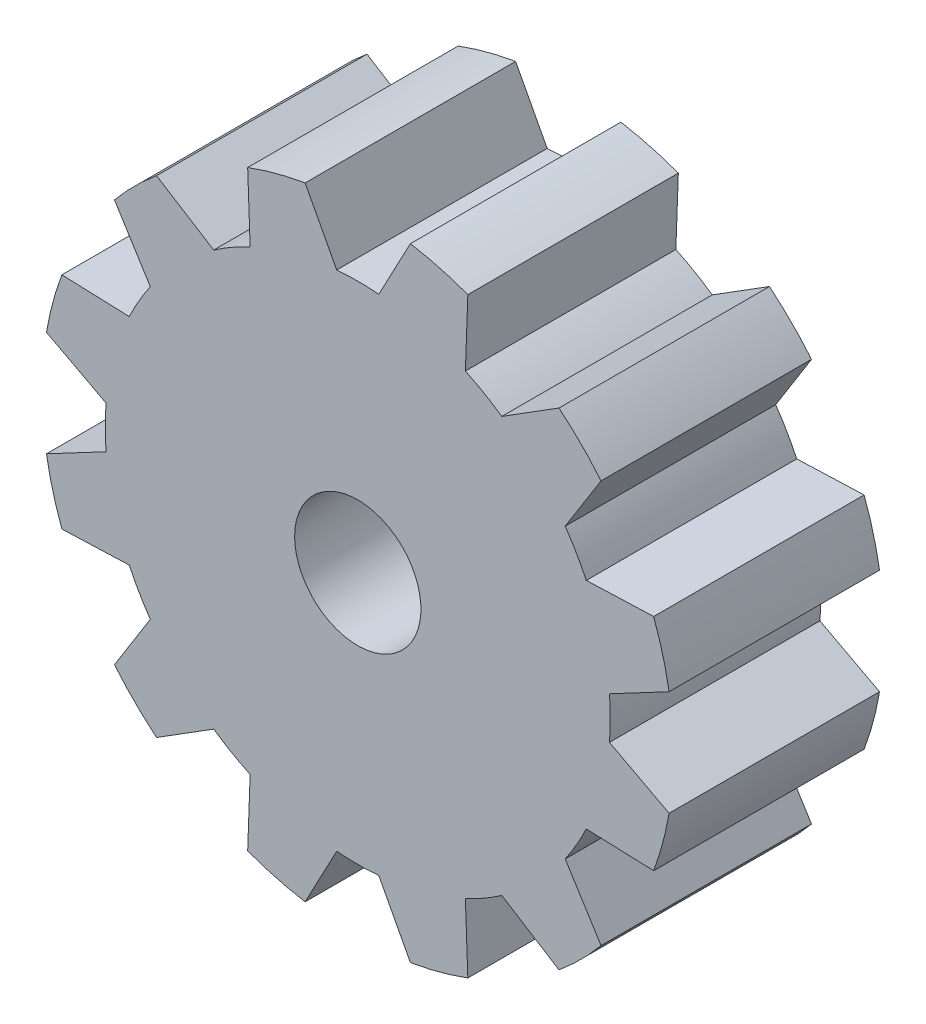
SolidWorks part; units mm, degrees
ref_plane "Front Plane" through (0, 0, 0) normal (0, 0, 1) x (1, 0, 0)
ref_plane "Top Plane" through (0, 0, 0) normal (0, 1, 0) x (1, 0, 0)
ref_plane "Right Plane" through (0, 0, 0) normal (1, 0, 0) x (0, 0, -1)
sketch "Sketch1" plane through (0, 0, 0) normal (0, 0, 1) x (1, 0, 0)
  circle A0 centre (0, 0) radius 15
  dimension "D1" = 30
extrude "Boss-Extrude1" add sketch "Sketch1" along normal blind 10
sketch "Sketch2" plane through (0, 0, 10) normal (0, 0, 1) x (1, 0, 0)
  line L0 (-1, 11.9583) -> (-2.5, 14.7902)
  line L1 (1, 11.9583) -> (2.5, 14.7902)
  line L2 (0, 0) -> (0, 15) construction
  line L3 (-2.5, 14.7902) -> (2.5, 14.7902) construction
  line L4 (1, 11.9583) -> (-1, 11.9583) construction
  circle A0 centre (0, 0) radius 15
  circle A1 centre (0, 0) radius 12
  point P8 (0, 7.5)
  point P10 (2.9269, 11.6376)
  circle M4 centre (0, 0) radius 15
  dimension "D1" = 30
  dimension "D2" = 24
  dimension "D3" = 5
  dimension "D4" = 2
extrude "Cut-Extrude1" cut sketch "Sketch2" against normal blind 10 contours A1 L1 L0 M4
pattern_circular "CirPattern1" count 12 every 30 about axis through (0, 0, 0) along (0, 0, 1) of "Cut-Extrude1"
sketch "Sketch3" plane through (0, 0, 0) normal (0, 0, -1) x (-1, 0, 0)
  circle A0 centre (0, 0) radius 3
extrude "Cut-Extrude2" cut sketch "Sketch3" against normal through all
